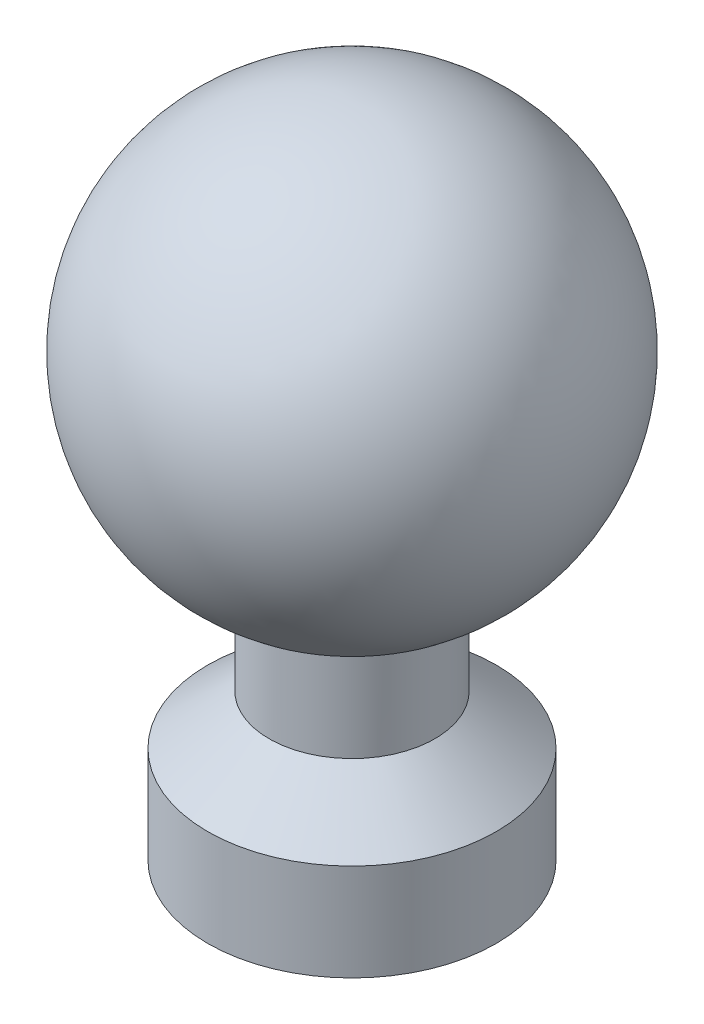
SolidWorks part; units mm, degrees
ref_plane "Plan de face" through (0, 0, 0) normal (0, 0, 1) x (1, 0, 0)
ref_plane "Plan de dessus" through (0, 0, 0) normal (0, 1, 0) x (1, 0, 0)
ref_plane "Plan de droite" through (0, 0, 0) normal (1, 0, 0) x (0, 0, -1)
sketch "Esquisse1" plane through (0, 0, 0) normal (0, 0, 1) x (1, 0, 0)
  line L0 (0, 34.3621) -> (0, 0)
  line L1 (4.4631, 14.0856) -> (4.4631, 7.8916)
  line L2 (4.4631, 7.8916) -> (7.7706, 5.2166)
  line L3 (7.7706, 5.2166) -> (7.7706, 0)
  line L4 (7.7706, 0) -> (0, 0)
  arc A0 (0, 34.3621) -> (4.4631, 14.0856) centre (0, 23.7326) cw
  point P1 (0, 0)
  point P4 (-1.2353, 12.5283)
  point P11 (0, 0)
  point P12 (0, 0.5799)
  point P13 (0, 0)
revolve "Révolution1" add sketch "Esquisse1" angle 360 about L0
surface "Surface-Décalage1" parameters "D1"=1
surface "Surface-Rétablir1"
ref_point "Point1"
sketch3d "Esquisse3D1"
  point P0 (1.277, 25.9629, 0.5195)
  point P1 (1.277, 25.9629, 0.5195)
